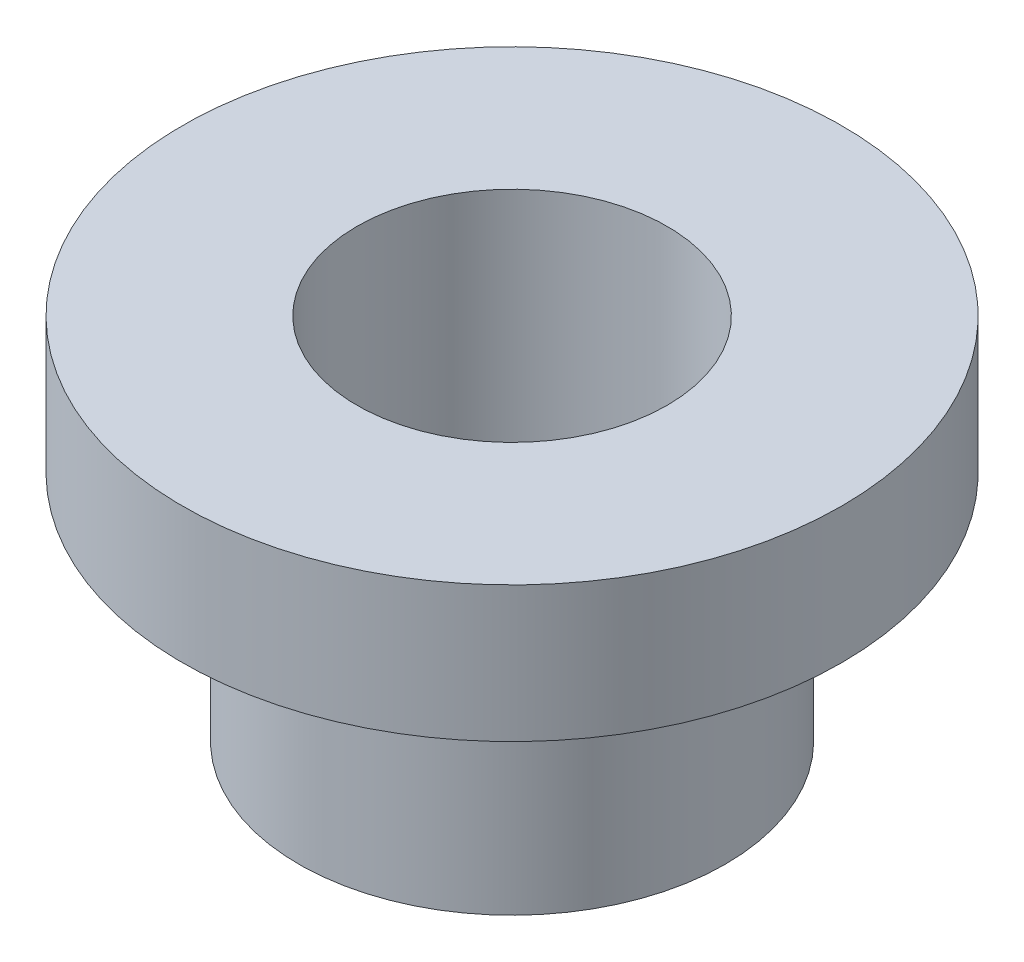
SolidWorks part; units mm, degrees
ref_plane "Alzado" through (0, 0, 0) normal (0, 0, 1) x (1, 0, 0)
ref_plane "Planta" through (0, 0, 0) normal (0, 1, 0) x (1, 0, 0)
ref_plane "Vista lateral" through (0, 0, 0) normal (1, 0, 0) x (0, 0, -1)
sketch "Croquis1" plane through (0, 0, 0) normal (0, 0, 1) x (1, 0, 0)
  line L0 (0, 0) -> (0, 19) construction
  line L1 (-8, 19) -> (-17, 19)
  line L2 (-17, 19) -> (-17, 12)
  line L3 (-17, 12) -> (-11, 12)
  line L4 (-11, 12) -> (-11, 0)
  line L5 (-11, 0) -> (-8, 0)
  line L6 (-8, 0) -> (-8, 19)
  dimension "D1" = 8
  dimension "D2" = 11
  dimension "D3" = 17
  dimension "D4" = 12
  dimension "D5" = 19
revolve "Revolución1" add sketch "Croquis1" angle 360 about L0
